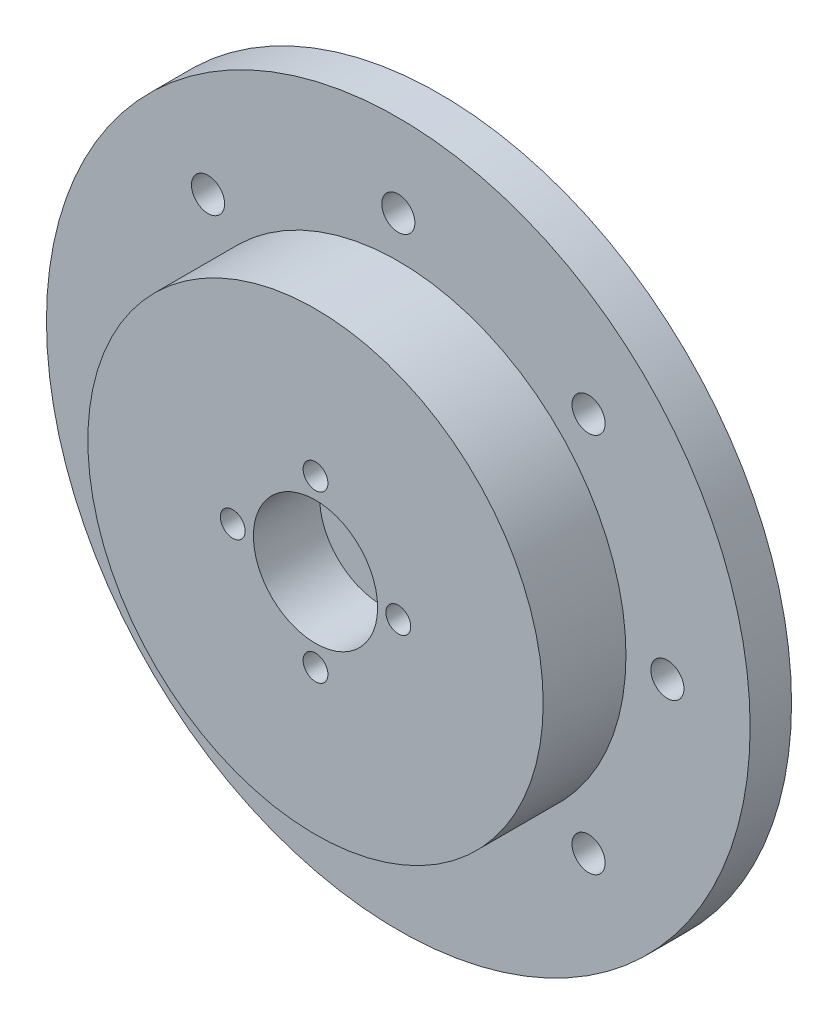
SolidWorks part; units mm, degrees
material "PET"
ref_plane "Front Plane" through (0, 0, 0) normal (0, 0, 1) x (1, 0, 0)
ref_plane "Top Plane" through (0, 0, 0) normal (0, 1, 0) x (1, 0, 0)
ref_plane "Right Plane" through (0, 0, 0) normal (1, 0, 0) x (0, 0, -1)
sketch "Sketch1" plane through (0, 0, 0) normal (0, 0, 1) x (1, 0, 0)
  circle A0 centre (0, 0) radius 42.5
  dimension "D1" = 85
extrude "Boss-Extrude1" add sketch "Sketch1" along normal blind 5
sketch "Sketch2" plane through (0, 0, 5) normal (0, 0, 1) x (1, 0, 0)
  circle A0 centre (0, 0) radius 27.5
  dimension "D1" = 55
extrude "Boss-Extrude2" add sketch "Sketch2" along normal blind 10
sketch "Sketch3" plane through (0, 0, 15) normal (0, 0, 1) x (1, 0, 0)
  circle A0 centre (0, 0) radius 7.5
  dimension "D1" = 15
extrude "Cut-Extrude1" cut sketch "Sketch3" against normal blind 8
sketch "Sketch4" plane through (0, 0, 15) normal (0, 0, 1) x (1, 0, 0)
  circle A0 centre (0, 0) radius 10 construction
  circle A1 centre (0, 10) radius 1.5
  circle A2 centre (10, 0) radius 1.5
  circle A3 centre (0, -10) radius 1.5
  circle A4 centre (-10, 0) radius 1.5
  point P14 (0, 0)
  dimension "D1" = 20
  dimension "D2" = 3
  dimension "D3" = 4
extrude "Cut-Extrude2" cut sketch "Sketch4" against normal through all
sketch "Sketch5" plane through (0, 0, 5) normal (0, 0, 1) x (1, 0, 0)
  circle A0 centre (0, 0) radius 32.5 construction
  circle A1 centre (0, 0) radius 27.5 construction
  circle A2 centre (0, 32.5) radius 2
  circle A3 centre (22.981, 22.981) radius 2
  circle A4 centre (32.5, 0) radius 2
  circle A5 centre (22.981, -22.981) radius 2
  circle A6 centre (0, -32.5) radius 2
  circle A7 centre (-22.981, -22.981) radius 2
  circle A8 centre (-32.5, 0) radius 2
  circle A9 centre (-22.981, 22.981) radius 2
  point P24 (0, 0)
  dimension "D1" = 5
  dimension "D2" = 4
  dimension "D3" = 8
extrude "Cut-Extrude3" cut sketch "Sketch5" against normal through all
